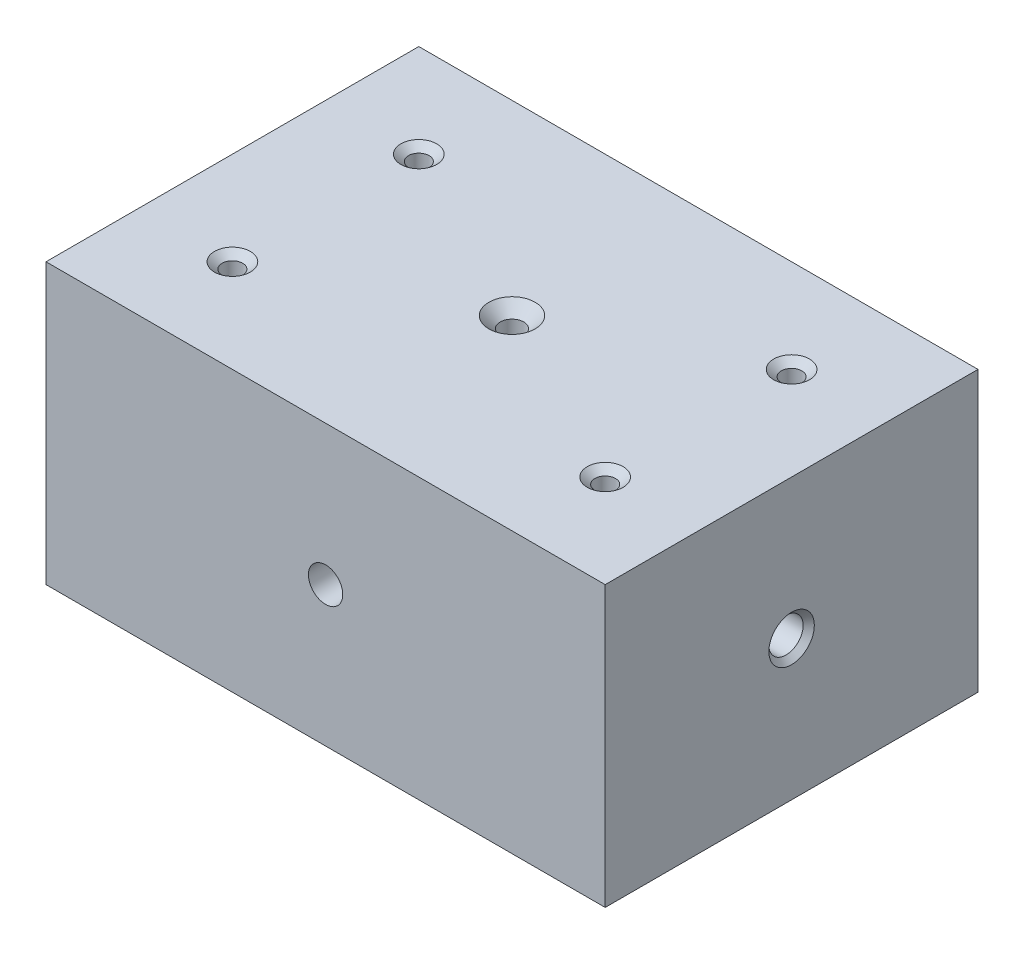
SolidWorks part; units mm, degrees
ref_plane "Front Plane" through (0, 0, 0) normal (0, 0, 1) x (1, 0, 0)
ref_plane "Top Plane" through (0, 0, 0) normal (0, 1, 0) x (1, 0, 0)
ref_plane "Right Plane" through (0, 0, 0) normal (1, 0, 0) x (0, 0, -1)
sketch "Sketch1" plane through (0, 0, 0) normal (0, 1, 0) x (1, 0, 0)
  line L1 (-76.2, 50.8) -> (76.2, 50.8)
  line L2 (-76.2, 50.8) -> (-76.2, -50.8)
  line L3 (-76.2, -50.8) -> (76.2, -50.8)
  line L4 (76.2, 50.8) -> (76.2, -50.8)
  line L5 (0, -50.8) -> (0, 50.8) construction
  line L6 (-76.2, 0) -> (76.2, 0) construction
  point P0 (0, 0)
  dimension "D1" = 101.6
  dimension "D2" = 152.4
extrude "Boss-Extrude1" add sketch "Sketch1" along normal blind 76.2
hole_wizard "CSK for #10 Flat Head Machine Screw (100)1" positions "Sketch4" profile "Sketch6" countersink size "#10" standard "ANSI Inch" end condition through all
sketch "Sketch4" plane through (0, 76.2, 0) normal (0, 1, 0) x (1, 0, 0)
  line L0 (-76.2, 50.8) -> (-76.2, -50.8) construction
  line L1 (76.2, 50.8) -> (-76.2, 50.8) construction
  line L4 (-76.2, 0) -> (76.2, 0) construction
  line L5 (76.2, -50.8) -> (76.2, 50.8) construction
  line L8 (0, 50.8) -> (0, -50.8) construction
  line L9 (-76.2, -50.8) -> (76.2, -50.8) construction
  point P0 (-50.8, 25.4)
  point P33 (-50.8, -25.4)
  point P34 (50.8, -25.4)
  point P35 (50.8, 25.4)
  dimension "D1" = 25.4
  dimension "D2" = 25.4
sketch "Sketch6" plane through (-50.8, 76.2, -25.4) normal (1, 0, 0) x (0, 0, 1)
  line L0 (0, 0) -> (0, 76.2)
  line L1 (0, 76.2) -> (2.8067, 76.2)
  line L2 (2.8067, 76.2) -> (2.8067, 1.7477)
  line L3 (2.8067, 1.7477) -> (4.8895, 0)
  line L5 (4.8895, 0) -> (0, 0)
  line L6 (-2.8067, 1.7477) -> (-4.8895, 0) construction
  line L11 (0, -6.35) -> (0, 107.95) construction
  dimension "Thru Hole Dia." = 5.6134
  dimension "Thru Hole Depth" = 76.2
  dimension "Near C'Sink Dia." = 9.779
  dimension "Near C'Sink Angle" = 100
hole_wizard "CSK for M6 Flat Head Machine Screw1" positions "Sketch7" profile "Sketch8" countersink size "M6" standard "ANSI Metric" end condition through all
sketch "Sketch7" plane through (0, 76.2, 0) normal (0, 1, 0) x (1, 0, 0)
  point P0 (0, 0)
sketch "Sketch8" plane through (0, 76.2, 0) normal (1, 0, 0) x (0, 0, 1)
  line L0 (0, 0) -> (0, 76.2)
  line L1 (0, 76.2) -> (3.2, 76.2)
  line L2 (3.2, 76.2) -> (3.2, 3.1)
  line L3 (3.2, 3.1) -> (6.3, 0)
  line L5 (6.3, 0) -> (0, 0)
  line L6 (-3.2, 3.1) -> (-6.3, 0) construction
  line L11 (0, -6.35) -> (0, 107.95) construction
  dimension "Thru Hole Dia." = 6.4
  dimension "Thru Hole Depth" = 76.2
  dimension "Near C'Sink Dia." = 12.6
  dimension "Near C'Sink Angle" = 90
hole_wizard "7/16-14 Tapped Hole3" positions "Sketch11" profile "Sketch10" tap size "7/16-14" standard "ANSI Inch"
sketch "Sketch11" plane through (76.2, 0, 0) normal (1, 0, 0) x (0, 0, -1)
  line L0 (-50.8, 38.1) -> (50.8, 38.1) construction
  line L1 (-50.8, 76.2) -> (-50.8, 0) construction
  line L2 (50.8, 76.2) -> (50.8, 0) construction
  point P0 (0, 38.1)
  point P12 (0, 38.1)
cosmetic thread "Hole Thread1" parameters "D1"=15.24, "D2"=11.1125
sketch "Sketch10" plane through (76.2, 38.1, 0) normal (0, 1, 0) x (0, 0, -1)
  line L0 (0, 0) -> (0, 23.3822)
  line L1 (0, 23.3822) -> (4.6736, 20.574)
  line L2 (4.6736, 20.574) -> (4.6736, 1.5177)
  line L3 (4.6736, 1.5177) -> (6.1913, 0)
  line L5 (6.1913, 0) -> (0, 0)
  line L6 (-4.6736, 1.5176) -> (-6.1913, 0) construction
  line L10 (0, 23.3822) -> (-4.6736, 20.574) construction
  line L11 (0, -6.35) -> (0, 107.95) construction
  dimension "Tap Drill Dia." = 9.3472
  dimension "Tap Drill Depth" = 20.574
  dimension "Near C'Sink Dia." = 12.3825
  dimension "Near C'Sink Angle" = 90
  dimension "Drill Angle" = 118
hole_wizard "7/16-14 Tapped Hole2" positions "Sketch12" profile "Sketch13" tap size "7/16-14" standard "ANSI Inch" end condition through all
sketch "Sketch12" plane through (0, 0, 50.8) normal (0, 0, 1) x (1, 0, 0)
  line L0 (-76.2, 38.1) -> (76.2, 38.1) construction
  line L1 (-76.2, 76.2) -> (-76.2, 0) construction
  line L2 (76.2, 76.2) -> (76.2, 0) construction
  point P0 (0, 38.1)
  point P13 (0, 38.1)
sketch "Sketch13" plane through (0, 38.1, 50.8) normal (1, 0, 0) x (0, -1, 0)
  line L0 (0, 0) -> (0, 101.6)
  line L1 (0, 101.6) -> (4.6736, 101.6)
  line L2 (4.6736, 101.6) -> (4.6736, 0)
  line L5 (4.6736, 0) -> (0, 0)
  line L11 (0, -6.35) -> (0, 107.95) construction
  dimension "Thru Tap Drill Dia." = 9.3472
  dimension "Thru Tap Drill Depth" = 101.6
cosmetic thread "Hole Thread2" parameters "D2"=11.1125
